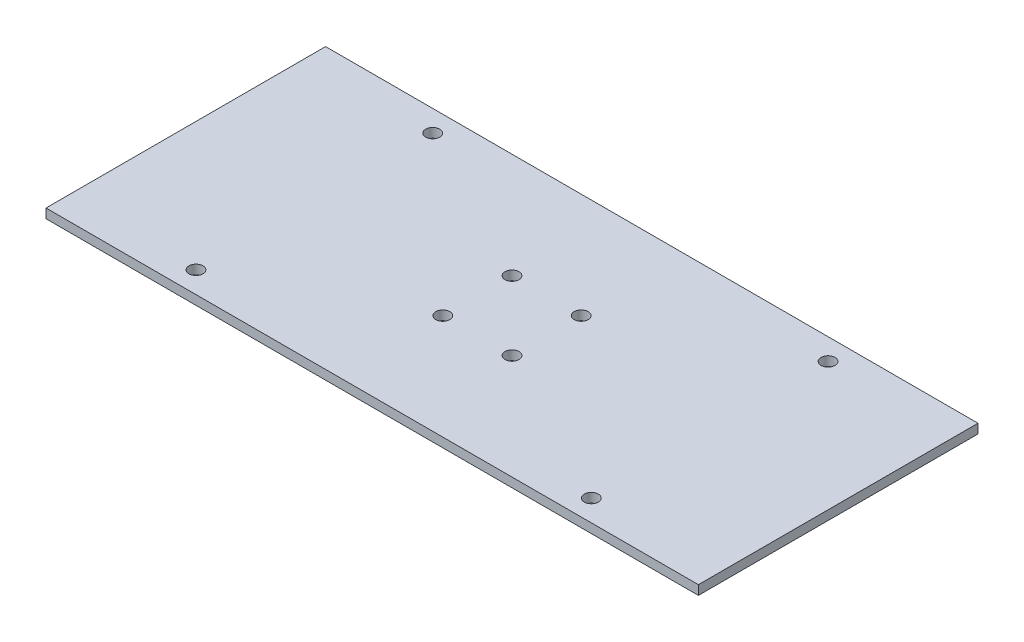
SolidWorks part; units mm, degrees
ref_plane "前视基准面" through (0, 0, 0) normal (0, 0, 1) x (1, 0, 0)
ref_plane "上视基准面" through (0, 0, 0) normal (0, 1, 0) x (1, 0, 0)
ref_plane "右视基准面" through (0, 0, 0) normal (1, 0, 0) x (0, 0, -1)
sketch "草图1" plane through (0, 0, 0) normal (0, 1, 0) x (1, 0, 0)
  line L0 (-55, 0) -> (55, 0) construction
  line L1 (-70, 30) -> (70, 30)
  line L2 (-70, 30) -> (-70, -30)
  line L3 (-70, -30) -> (70, -30)
  line L4 (70, 30) -> (70, -30)
  line L5 (-70, 30) -> (70, -30) construction
  line L6 (-70, -30) -> (70, 30) construction
  line L7 (0, -55) -> (0, 55) construction
  circle A0 centre (-42.42, 25.4) radius 1.5
  circle A1 centre (-42.42, -25.4) radius 1.5
  circle A2 centre (42.42, -25.4) radius 1.5
  circle A3 centre (42.42, 25.4) radius 1.5
  circle A4 centre (-7.425, 7.425) radius 1.5
  circle A5 centre (7.425, 7.425) radius 1.5
  circle A6 centre (7.425, -7.425) radius 1.5
  circle A7 centre (-7.425, -7.425) radius 1.5
  point P0 (0, 0)
  point P29 (0, 0)
  dimension "D3" = 42.42
  dimension "D4" = 3
  dimension "D5" = 25.4
  dimension "D6" = 3
  dimension "D7" = 7.425
  dimension "D8" = 7.425
  dimension "D1" = 140
  dimension "D2" = 60
  dimension "D9" = 4
extrude "凸台-拉伸1" add sketch "草图1" along normal blind 2
